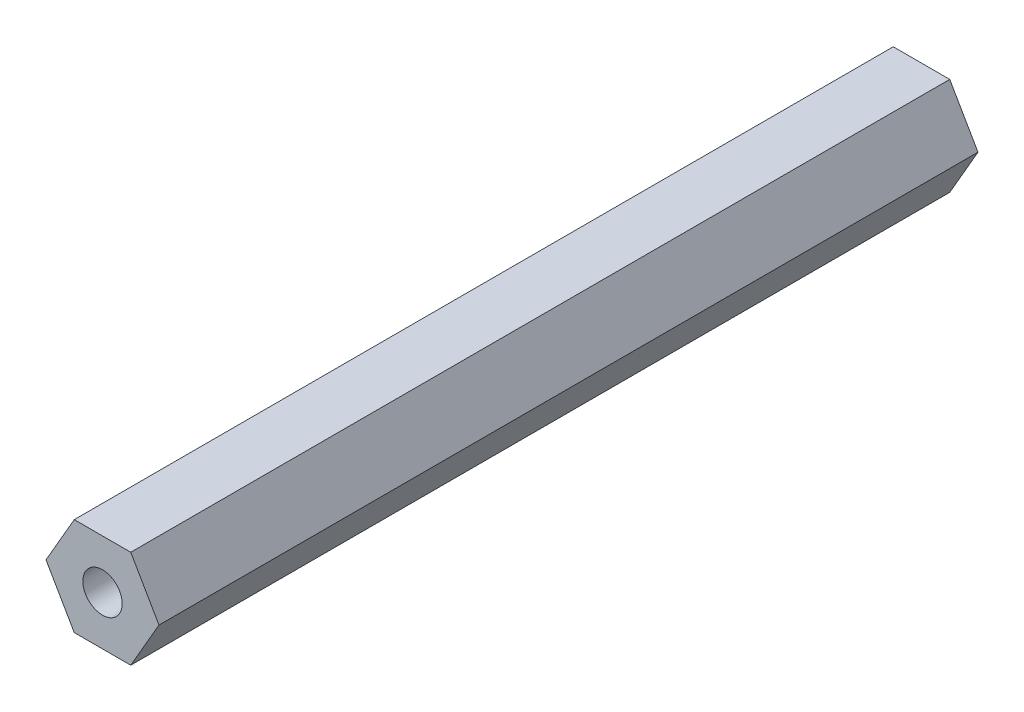
SolidWorks part; units mm, degrees
material "6061-T6 (SS)"
ref_plane "Front Plane" through (0, 0, 0) normal (0, 0, 1) x (1, 0, 0)
ref_plane "Top Plane" through (0, 0, 0) normal (0, 1, 0) x (1, 0, 0)
ref_plane "Right Plane" through (0, 0, 0) normal (1, 0, 0) x (0, 0, -1)
sketch "Sketch1" plane through (0, 0, 0) normal (0, 0, 1) x (1, 0, 0)
  line L1 (3.6662, -6.35) -> (7.3323, 0)
  line L2 (7.3323, 0) -> (3.6662, 6.35)
  line L3 (3.6662, 6.35) -> (-3.6662, 6.35)
  line L4 (-3.6662, 6.35) -> (-7.3323, 0)
  line L5 (-7.3323, 0) -> (-3.6662, -6.35)
  line L6 (-3.6662, -6.35) -> (3.6662, -6.35)
  circle A0 centre (0, 0) radius 6.35 construction
  dimension "D1" = 12.7
extrude "Boss-Extrude1" add sketch "Sketch1" along normal blind 106.299
hole_wizard "1/4-20 Tapped Hole1" positions "Sketch2" profile "Sketch3" tap size "1/4-20" standard "ANSI Inch" end condition through all
sketch "Sketch2" plane through (0, 0, 0) normal (0, 0, -1) x (-1, 0, 0)
  point P0 (0, 0)
sketch "Sketch3" plane through (0, 0, 0) normal (1, 0, 0) x (0, 1, 0)
  line L0 (0, 0) -> (0, 106.299)
  line L1 (0, 106.299) -> (2.5527, 106.299)
  line L2 (2.5527, 106.299) -> (2.5527, 0)
  line L5 (2.5527, 0) -> (0, 0)
  line L11 (0, -6.35) -> (0, 107.95) construction
  dimension "Thru Tap Drill Dia." = 5.1054
  dimension "Thru Tap Drill Depth" = 106.299
cosmetic thread "Hole Thread1" parameters "D2"=6.35
equation "\"Thick\"= \"in\""
